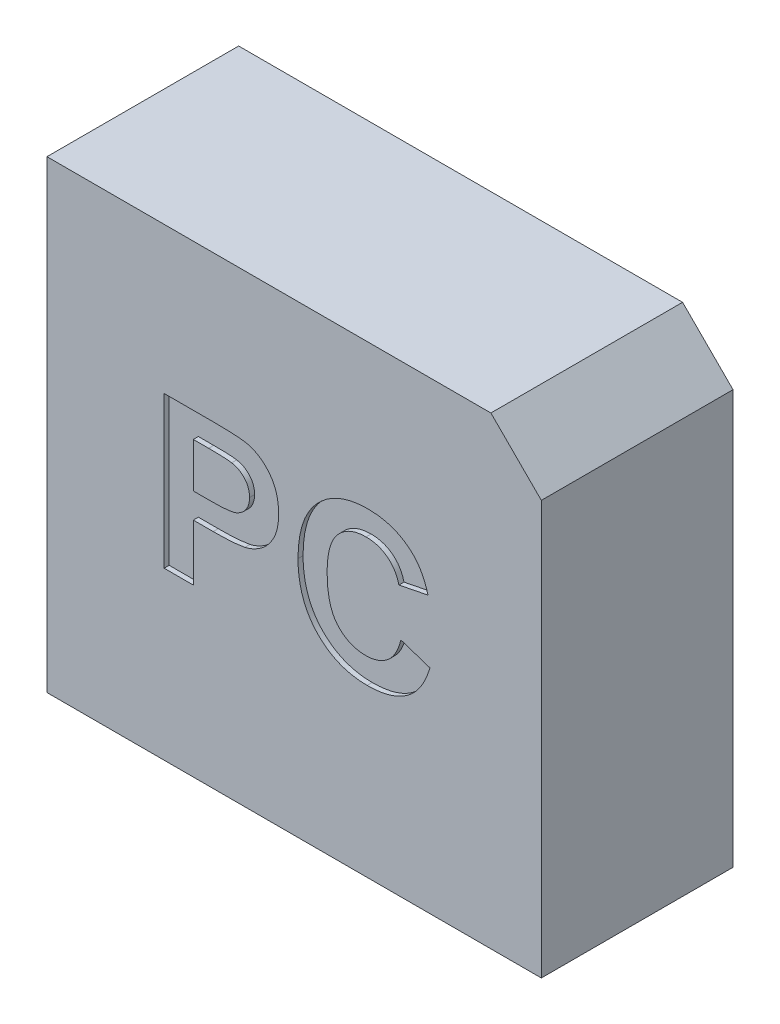
SolidWorks part; units mm, degrees
ref_plane "Front Plane" through (0, 0, 0) normal (0, 0, 1) x (1, 0, 0)
ref_plane "Top Plane" through (0, 0, 0) normal (0, 1, 0) x (1, 0, 0)
ref_plane "Right Plane" through (0, 0, 0) normal (1, 0, 0) x (0, 0, -1)
sketch "Sketch1" plane through (0, 0, 0) normal (0, 1, 0) x (1, 0, 0)
  line L1 (-245, 95) -> (245, 95)
  line L2 (-245, 95) -> (-245, -95)
  line L3 (-245, -95) -> (245, -95)
  line L4 (245, 95) -> (245, -95)
  line L5 (-245, 95) -> (245, -95) construction
  line L6 (-245, -95) -> (245, 95) construction
  point P0 (0, 0)
  dimension "D1" = 190
  dimension "D2" = 490
extrude "Boss-Extrude1" add sketch "Sketch1" along normal blind 460
sketch "Sketch2" plane through (0, 0, 95) normal (0, 0, 1) x (1, 0, 0)
  line L0 (-245, 164.8132) -> (245, 164.8132) construction
  line L1 (-245, 460) -> (-245, 0) construction
  line L2 (245, 460) -> (245, 0) construction
  text T0 "PC" font "Arial" height 150
extrude "Cut-Extrude1" cut sketch "Sketch2" against normal blind 5
chamfer "Chamfer1" distance 50 angle 45 1 edges at (245, 460, 0)
